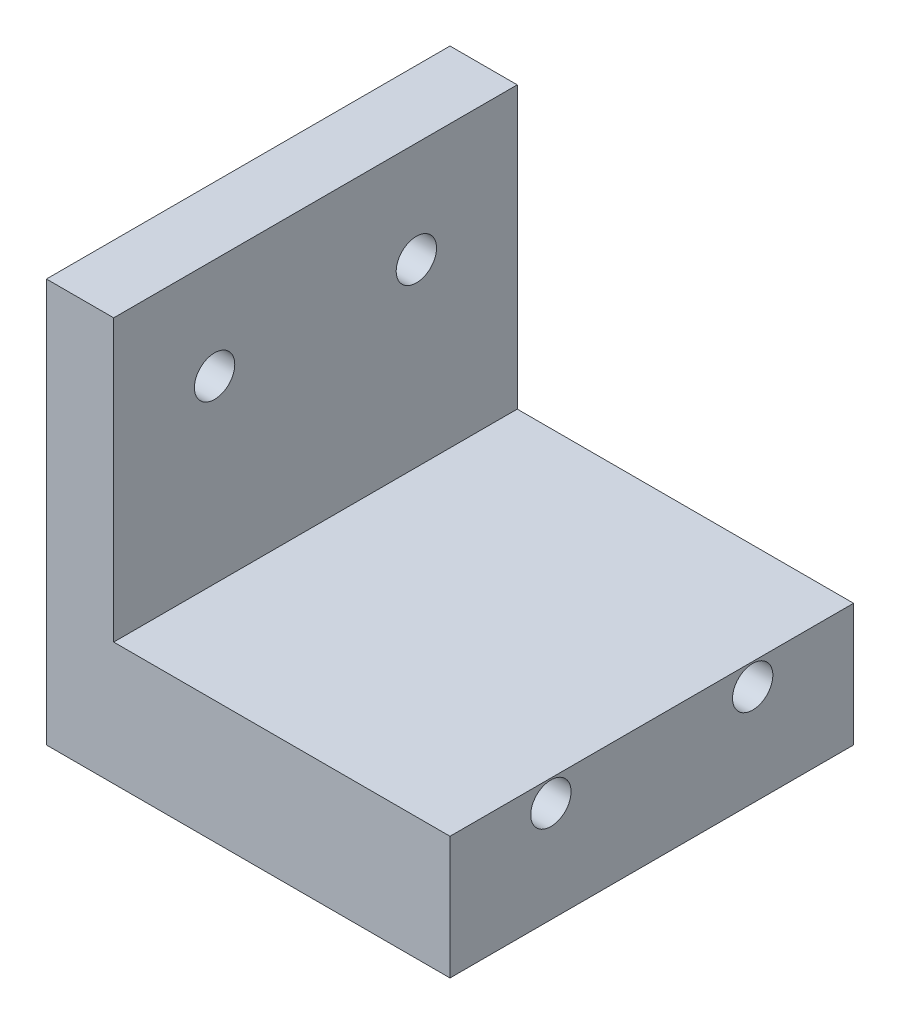
SolidWorks part; units mm, degrees
ref_plane "Front Plane" through (0, 0, 0) normal (0, 0, 1) x (1, 0, 0)
ref_plane "Top Plane" through (0, 0, 0) normal (0, 1, 0) x (1, 0, 0)
ref_plane "Right Plane" through (0, 0, 0) normal (1, 0, 0) x (0, 0, -1)
sketch "Sketch1" plane through (0, 0, 0) normal (0, 1, 0) x (1, 0, 0)
  line L1 (-30, 30) -> (30, 30)
  line L2 (-30, 30) -> (-30, -30)
  line L3 (-30, -30) -> (30, -30)
  line L4 (30, 30) -> (30, -30)
  line L5 (-30, 30) -> (30, -30) construction
  line L6 (-30, -30) -> (30, 30) construction
  point P0 (0, 0)
  dimension "D1" = 60
  dimension "D2" = 60
extrude "Boss-Extrude1" add sketch "Sketch1" along normal blind 60
sketch "Sketch2" plane through (30, 0, 0) normal (1, 0, 0) x (0, 0, -1)
  line L0 (0, 60) -> (0, 0) construction
  line L1 (-30, 60) -> (30, 60) construction
  line L2 (-30, 30) -> (30, 30) construction
  line L3 (-30, 60) -> (-30, 0) construction
  line L4 (30, 60) -> (30, 0) construction
  line L6 (-15, 45) -> (15, 45)
  line L7 (-15, 45) -> (-15, 15)
  line L8 (-15, 15) -> (15, 15)
  line L9 (15, 45) -> (15, 15)
  line L10 (-15, 45) -> (15, 15) construction
  line L11 (-15, 15) -> (15, 45) construction
  circle A0 centre (-15, 45) radius 3
  point P11 (0, 30)
  dimension "D3" = 6
  dimension "D1" = 30
  dimension "D2" = 30
extrude "Cut-Extrude1" cut sketch "Sketch2" against normal through all contours A0
pattern_linear "LPattern1" count 2 spacing 30 along (0, 0, -1) count 2 spacing 30 along (0, -1, 0) of "Cut-Extrude1"
sketch "Sketch4" plane through (0, 0, -30) normal (0, 0, -1) x (-1, 0, 0)
  line L0 (0, 60) -> (0, 0) construction
  line L1 (-30, 60) -> (30, 60) construction
  line L2 (-30, 0) -> (30, 0) construction
  line L3 (-30, 30) -> (30, 30) construction
  line L4 (-30, 60) -> (-30, 0) construction
  line L5 (30, 60) -> (30, 0) construction
  line L7 (-20, 60) -> (20, 60)
  line L8 (-20, 60) -> (-20, 18.25)
  line L9 (-20, 18.25) -> (20, 18.25)
  line L10 (20, 60) -> (20, 18.25)
  dimension "D1" = 10
  dimension "D2" = 10
  dimension "D3" = 18.25
extrude "Cut-Extrude3" cut sketch "Sketch4" against normal up to next
sketch "Sketch6" plane through (0, 0, 30) normal (0, 0, 1) x (1, 0, 0)
  line L1 (30, 60) -> (20, 60)
  line L2 (30, 60) -> (30, 18.25)
  line L3 (30, 18.25) -> (20, 18.25)
  line L4 (20, 60) -> (20, 18.25)
extrude "Cut-Extrude5" cut sketch "Sketch6" against normal up to next
sketch "Sketch7" plane through (0, 18.25, 0) normal (0, 1, 0) x (1, 0, 0)
  line L0 (-20, 0) -> (30, 0) construction
  line L1 (-20, -30) -> (-20, 30) construction
  line L2 (30, 30) -> (30, -30) construction
  line L3 (30, 0) -> (-13.3013, 25) construction
  line L4 (-15.6433, 20.9435) -> (27.658, -4.0565)
  line L5 (-15.6433, 20.9435) -> (-10.9593, 29.0565)
  line L6 (27.658, -4.0565) -> (32.342, 4.0565)
  line L7 (-10.9593, 29.0565) -> (32.342, 4.0565)
  line L8 (-15.6433, 20.9435) -> (32.342, 4.0565) construction
  line L9 (27.658, -4.0565) -> (-10.9593, 29.0565) construction
  point P8 (8.3494, 12.5)
  dimension "D1" = 30
  dimension "D2" = 50
